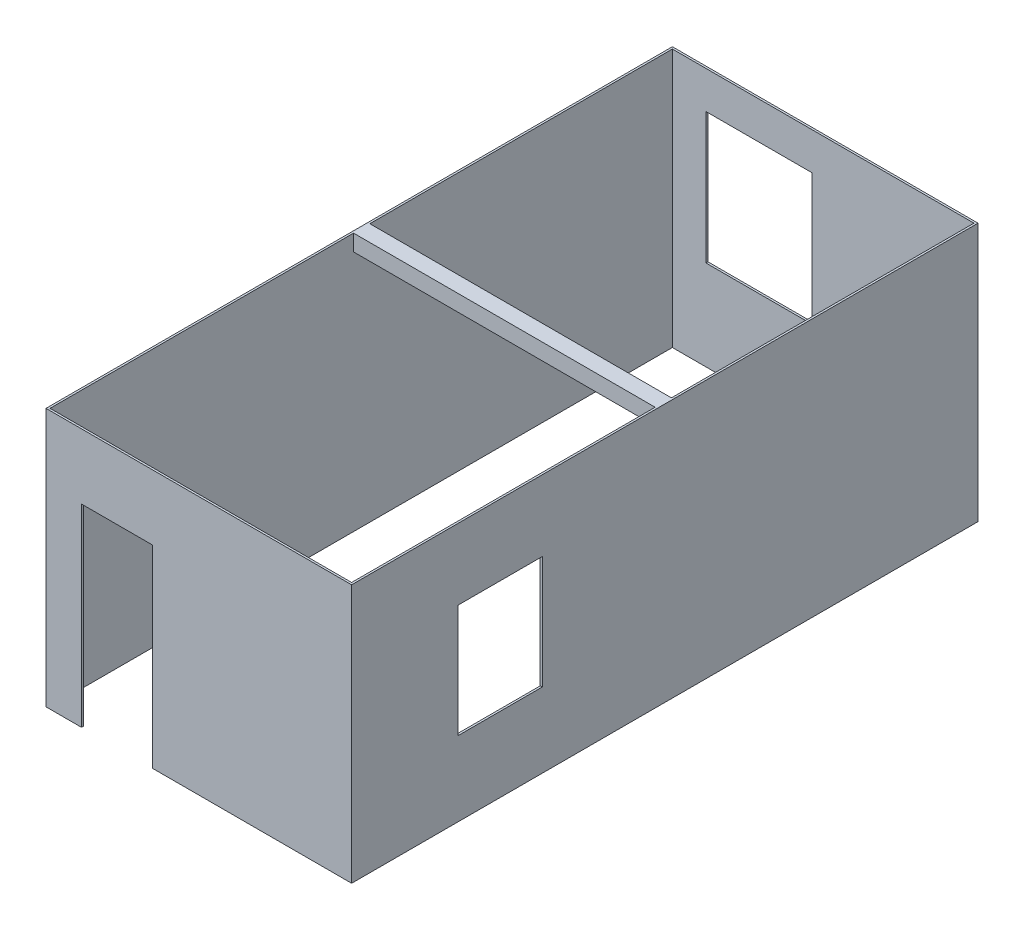
SolidWorks part; units mm, degrees
material "屋面瓦"
ref_plane "前视基准面" through (0, 0, 0) normal (0, 0, 1) x (1, 0, 0)
ref_plane "上视基准面" through (0, 0, 0) normal (0, 1, 0) x (1, 0, 0)
ref_plane "右视基准面" through (0, 0, 0) normal (1, 0, 0) x (0, 0, -1)
sketch "草图1" plane through (0, 0, 0) normal (0, 1, 0) x (1, 0, 0)
  line L1 (0, 0) -> (-3150, 0)
  line L2 (0, 0) -> (0, 6500)
  line L3 (0, 6500) -> (-3150, 6500)
  line L4 (-3150, 0) -> (-3150, 6500)
  dimension "D1" = 6500
  dimension "D2" = 3150
extrude "墙" add sketch "草图1" along normal blind 2700 thin thin type one direction wall 21
sketch "草图2" plane through (0, 0, 0) normal (0, 0, -1) x (-1, 0, 0)
  line L0 (3150, 0) -> (0, 0) construction
  line L1 (2800, 0) -> (2060, 0)
  line L2 (2800, 0) -> (2800, 2020)
  line L3 (2800, 2020) -> (2060, 2020)
  line L4 (2060, 0) -> (2060, 2020)
  dimension "D1" = 350
  dimension "D2" = 740
  dimension "D3" = 2020
extrude "门" cut sketch "草图2" against normal through all
sketch "草图3" plane through (0, 0, 0) normal (-1, 0, 0) x (0, 0, 1)
  line L0 (0, 2700) -> (0, 0) construction
  line L1 (-1970, 1960) -> (-1090, 1960)
  line L2 (-1970, 1960) -> (-1970, 780)
  line L3 (-1970, 780) -> (-1090, 780)
  line L4 (-1090, 1960) -> (-1090, 780)
  line L5 (0, 0) -> (-6500, 0) construction
  dimension "D1" = 1090
  dimension "D2" = 880
  dimension "D3" = 780
  dimension "D4" = 1180
extrude "窗1" cut sketch "草图3" against normal through all
sketch "草图4" plane through (0, 0, -6500) normal (0, 0, 1) x (1, 0, 0)
  line L0 (-3150, 2700) -> (-3150, 0) construction
  line L1 (-2800, 2310) -> (-1690, 2310)
  line L2 (-2800, 2310) -> (-2800, 940)
  line L3 (-2800, 940) -> (-1690, 940)
  line L4 (-1690, 2310) -> (-1690, 940)
  line L5 (0, 0) -> (-3150, 0) construction
  dimension "D1" = 1370
  dimension "D2" = 1110
  dimension "D3" = 350
  dimension "D4" = 940
extrude "窗2" cut sketch "草图4" against normal through all
sketch "草图5" plane through (0, 0, 0) normal (-1, 0, 0) x (0, 0, 1)
  line L0 (0, 2700) -> (-6500, 2700) construction
  line L1 (-3340, 2700) -> (-3170, 2700)
  line L2 (-3340, 2700) -> (-3340, 2530)
  line L3 (-3340, 2530) -> (-3170, 2530)
  line L4 (-3170, 2700) -> (-3170, 2530)
  line L5 (-1970, 1960) -> (-1970, 780) construction
  dimension "D1" = 170
  dimension "D2" = 170
  dimension "D3" = 1200
extrude "横梁" add sketch "草图5" along normal up to next
